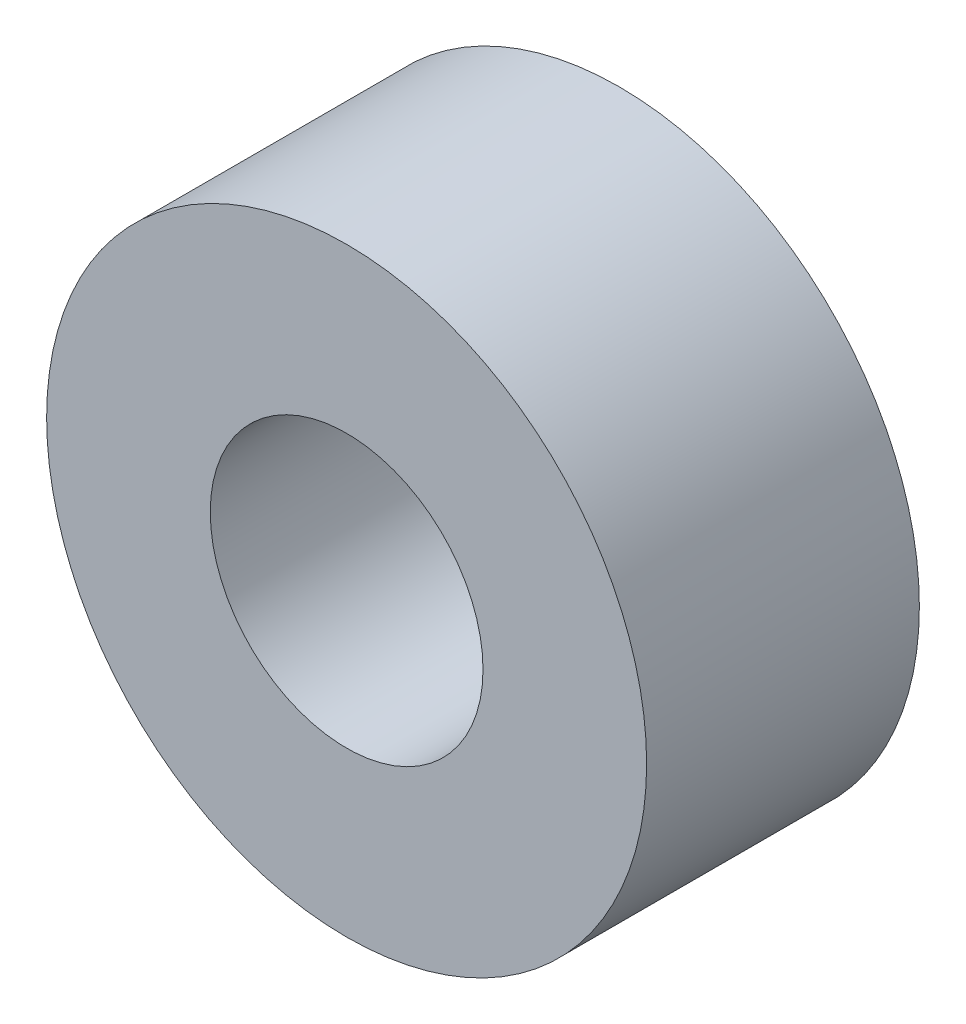
SolidWorks part; units mm, degrees
ref_plane "Front Plane" through (0, 0, 0) normal (0, 0, 1) x (1, 0, 0)
ref_plane "Top Plane" through (0, 0, 0) normal (0, 1, 0) x (1, 0, 0)
ref_plane "Right Plane" through (0, 0, 0) normal (1, 0, 0) x (0, 0, -1)
sketch "Sketch1" plane through (0, 0, 0) normal (0, 0, 1) x (1, 0, 0)
  circle A0 centre (0, 0) radius 2.5
  circle A1 centre (0, 0) radius 5.5
extrude "Boss-Extrude1" add sketch "Sketch1" along normal blind 5
